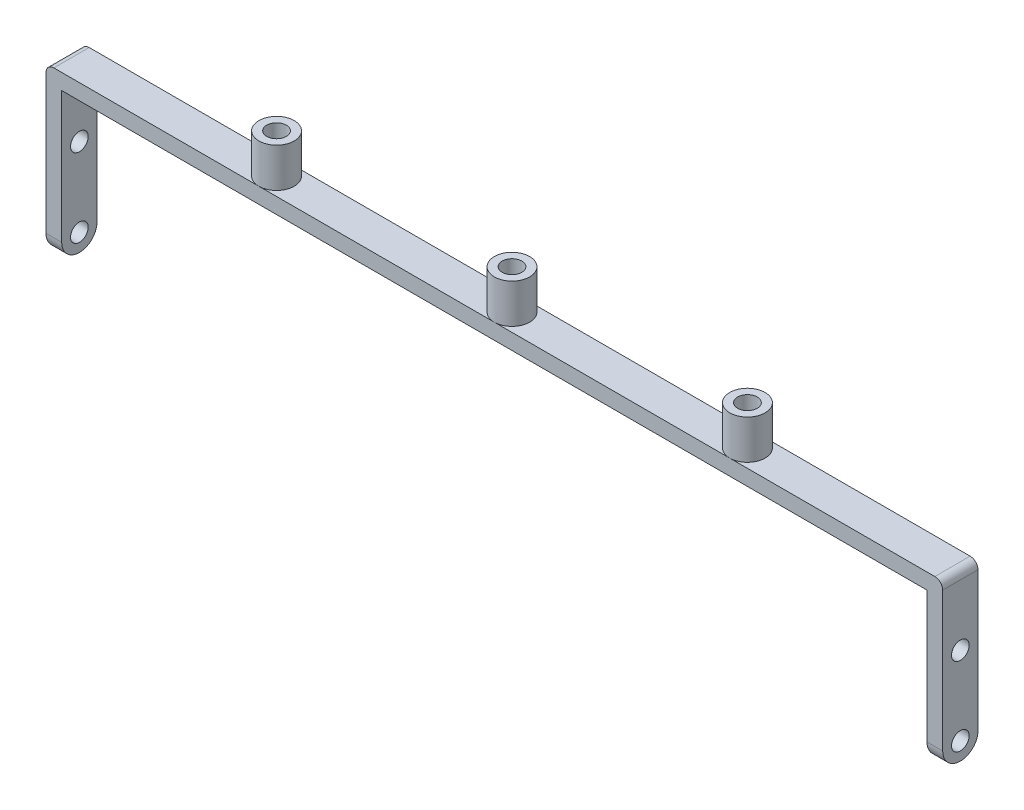
SolidWorks part; units mm, degrees
ref_plane "Front Plane" through (0, 0, 0) normal (0, 0, 1) x (1, 0, 0)
ref_plane "Top Plane" through (0, 0, 0) normal (0, 1, 0) x (1, 0, 0)
ref_plane "Right Plane" through (0, 0, 0) normal (1, 0, 0) x (0, 0, -1)
sketch "Sketch1" plane through (0, 0, 0) normal (0, 0, 1) x (1, 0, 0)
  line L0 (-110.25, 0) -> (110.25, 0)
  line L1 (-110.25, 0) -> (-110.25, -38)
  line L2 (110.25, 0) -> (110.25, -38)
  line L3 (114.25, 4) -> (114.25, -38)
  line L4 (-114.25, 4) -> (114.25, 4)
  line L5 (-114.25, 4) -> (-114.25, -38)
  line L6 (-114.25, -38) -> (-110.25, -38)
  line L7 (110.25, -38) -> (114.25, -38)
  point P4 (0, 0)
  dimension "D1" = 220.5
  dimension "D2" = 38
  dimension "D3" = 38
  dimension "D4" = 4
extrude "Boss-Extrude1" add sketch "Sketch1" along normal blind 9
sketch "Sketch2" plane through (114.25, 0, 0) normal (1, 0, 0) x (0, 0, -1)
  line L0 (-9, -38) -> (0, -38) construction
  line L1 (-9, -33.5) -> (-9, -38)
  line L2 (-9, -38) -> (0, -38)
  line L3 (0, -38) -> (0, -33.5)
  circle A0 centre (-4.5, -33.5) radius 4.5
  circle A1 centre (-4.5, -33.5) radius 2.25
  circle A2 centre (-4.5, -13.5) radius 4.5
  circle A3 centre (-4.5, -13.5) radius 2.25
  line M2 (0, -38) -> (0, 4)
  line M4 (-9, 4) -> (-9, -38)
  line M5 (-9, -38) -> (0, -38)
  dimension "D1" = 9
  dimension "D2" = 4.5
  dimension "D3" = 4.5
  dimension "D4" = 20
extrude "Cut-Extrude1" cut sketch "Sketch2" against normal through all contours A3 | A0 M4 M5 | A0 L2 M2 | A1
fillet "Fillet1" radius 2 2 edges at (114.25, 4, 4.5) (-114.25, 4, 4.5)
sketch "Sketch3" plane through (0, 4, 0) normal (0, 1, 0) x (1, 0, 0)
  line L0 (-112.25, -4.5) -> (112.25, -4.5) construction
  line L1 (-112.25, 0) -> (-112.25, -9) construction
  line L2 (112.25, -9) -> (112.25, 0) construction
  circle A0 centre (0, -4.5) radius 4.5
  circle A1 centre (60, -4.5) radius 4.5
  circle A2 centre (-60, -4.5) radius 4.5
  circle A3 centre (0, -4.5) radius 2.5
  circle A4 centre (60, -4.5) radius 2.5
  circle A5 centre (-60, -4.5) radius 2.5
  dimension "D1" = 5
  dimension "D2" = 5
  dimension "D3" = 5
  dimension "D4" = 60
  dimension "D5" = 60
extrude "Boss-Extrude2" add sketch "Sketch3" along normal blind 10
